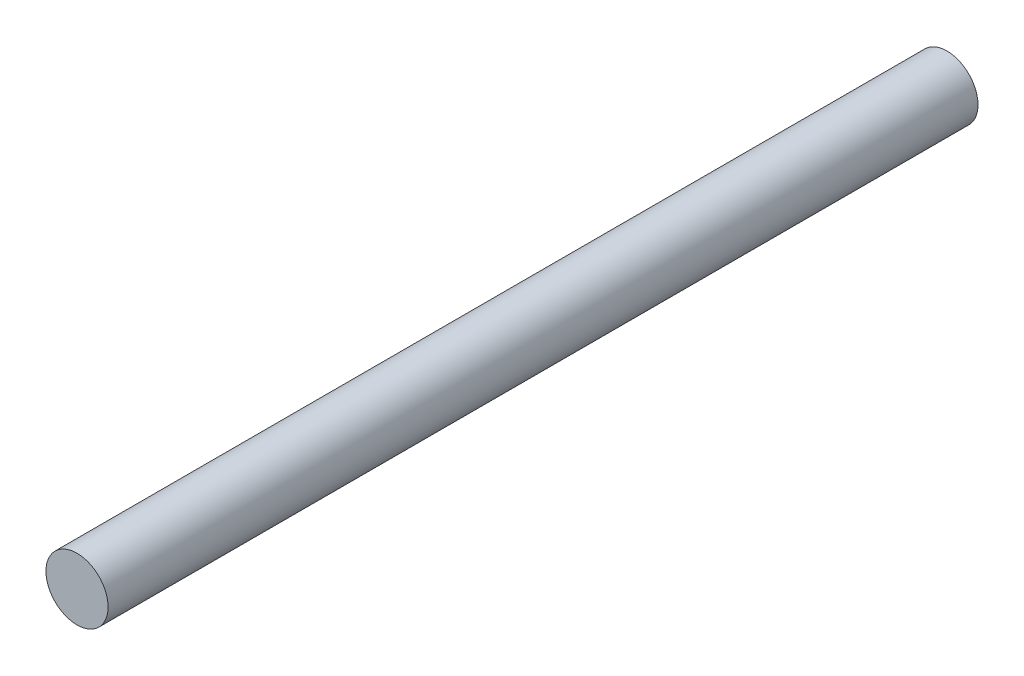
SolidWorks part; units mm, degrees
ref_plane "正面" through (0, 0, 0) normal (0, 0, 1) x (1, 0, 0)
ref_plane "平面" through (0, 0, 0) normal (0, 1, 0) x (1, 0, 0)
ref_plane "右側面" through (0, 0, 0) normal (1, 0, 0) x (0, 0, -1)
sketch "ｽｹｯﾁ1" plane through (0, 0, 0) normal (0, 0, 1) x (1, 0, 0)
  circle A0 centre (0, 0) radius 2.5
  dimension "D1" = 5
extrude "ﾎﾞｽ - 押し出し1" add sketch "ｽｹｯﾁ1" along normal blind 70
